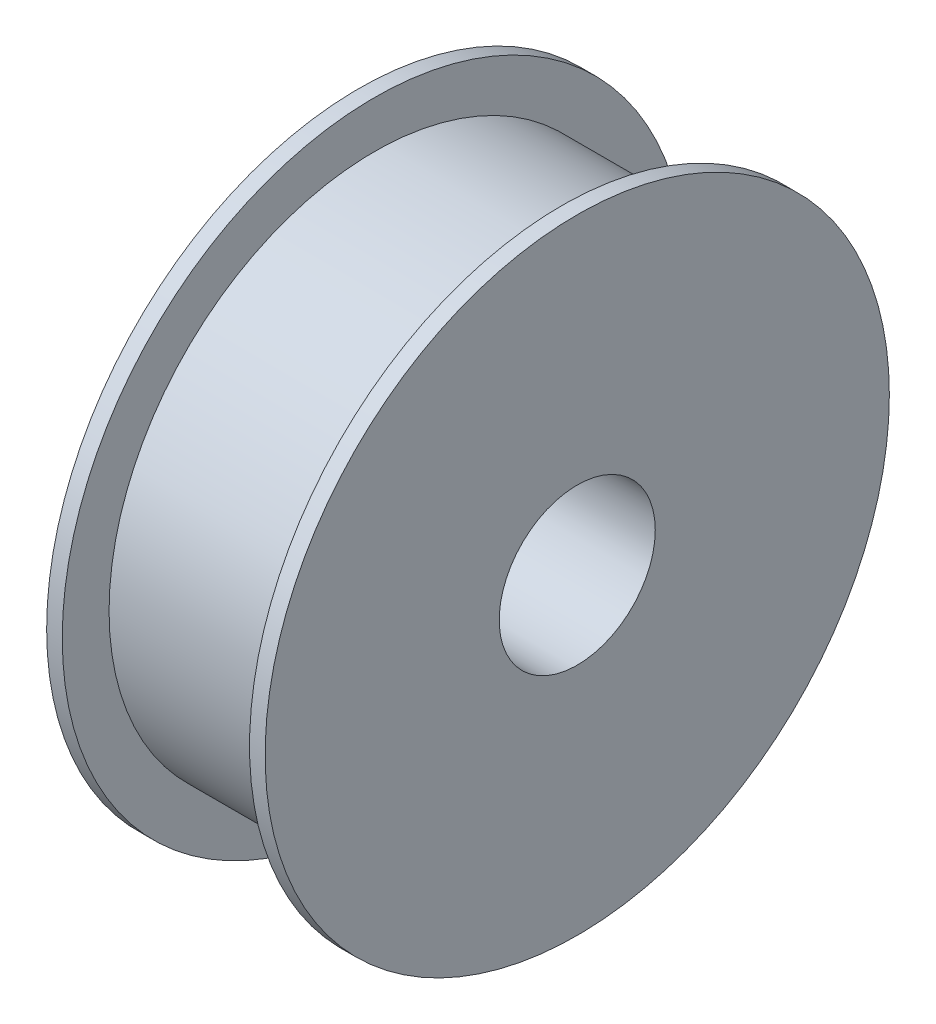
SolidWorks part; units mm, degrees
ref_plane "Alzado" through (0, 0, 0) normal (0, 0, 1) x (1, 0, 0)
ref_plane "Planta" through (0, 0, 0) normal (0, 1, 0) x (1, 0, 0)
ref_plane "Vista lateral" through (0, 0, 0) normal (1, 0, 0) x (0, 0, -1)
sketch "Croquis1" plane through (0, 0, 0) normal (1, 0, 0) x (0, 0, -1)
  circle A0 centre (0, 0) radius 100
  circle A1 centre (0, 0) radius 25
  dimension "D1" = 200
  dimension "D2" = 50
extrude "Saliente-Extruir1" add sketch "Croquis1" along normal blind 5
sketch "Croquis2" plane through (0, 0, 0) normal (-1, 0, 0) x (0, 0, 1)
  circle A0 centre (0, 0) radius 85
  dimension "D1" = 170
extrude "Saliente-Extruir2" add sketch "Croquis2" along normal blind 60
sketch "Croquis3" plane through (-60, 0, 0) normal (-1, 0, 0) x (0, 0, 1)
  circle A0 centre (0, 0) radius 100
  dimension "D1" = 200
extrude "Saliente-Extruir3" add sketch "Croquis3" along normal blind 5
sketch "Croquis4" plane through (0, 0, 0) normal (1, 0, 0) x (0, 0, -1)
  circle A1 centre (0, 0) radius 25
  circle A2 centre (0, 0) radius 25
  dimension "D1" = 0
extrude "Cortar-Extruir1" cut sketch "Croquis4" against normal blind 65
